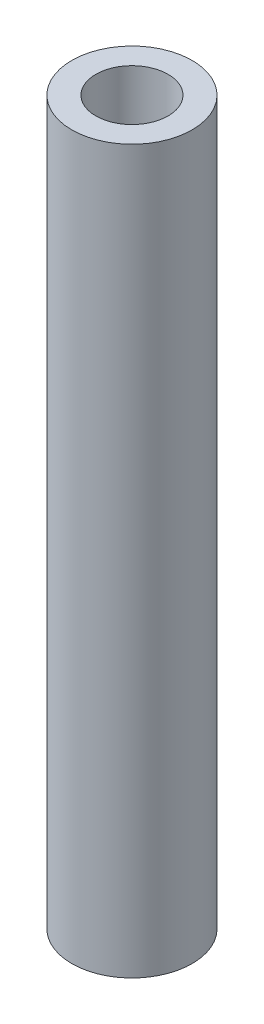
SolidWorks part; units mm, degrees
ref_plane "Front Plane" through (0, 0, 0) normal (0, 0, 1) x (1, 0, 0)
ref_plane "Top Plane" through (0, 0, 0) normal (0, 1, 0) x (1, 0, 0)
ref_plane "Right Plane" through (0, 0, 0) normal (1, 0, 0) x (0, 0, -1)
sketch "Sketch1" plane through (0, 0, 0) normal (0, 1, 0) x (1, 0, 0)
  circle A0 centre (0, 0) radius 2.5
  circle A1 centre (0, 0) radius 1.5
  dimension "D1" = 3
  dimension "D2" = 5
extrude "Boss-Extrude1" add sketch "Sketch1" along normal blind 30
thread "Thread1" pitch 0.5 start angle 0, offset 1, length 0, pitch 0.5, diameter 3
ref_plane "Plane1" through (-1.5, 41, 0) normal (0, 0, 1) x (-1, 0, 0)
sketch "Thread Profile1" plane through (-1.5, 41, 0) normal (0, 0, 1) x (-1, 0, 0)
  line L0 (0, 0) -> (0, 0.5) construction
  line L1 (0, 0) -> (0.2706, 0.1562)
  line L2 (0.2706, 0.1562) -> (0.2706, 0.2187)
  line L3 (0.2706, 0.2187) -> (0, 0.375)
  line L4 (0.2706, 0.1875) -> (0, 0.1875) construction
  line L11 (0, 0) -> (0, 0.375)
  point P2 (0, 0)
  dimension "Pitch" = 0.5
  dimension "Profile_Angle" = 60
  dimension "Profile_Land" = 0.0625
  dimension "Profile_Height" = 0.2706
